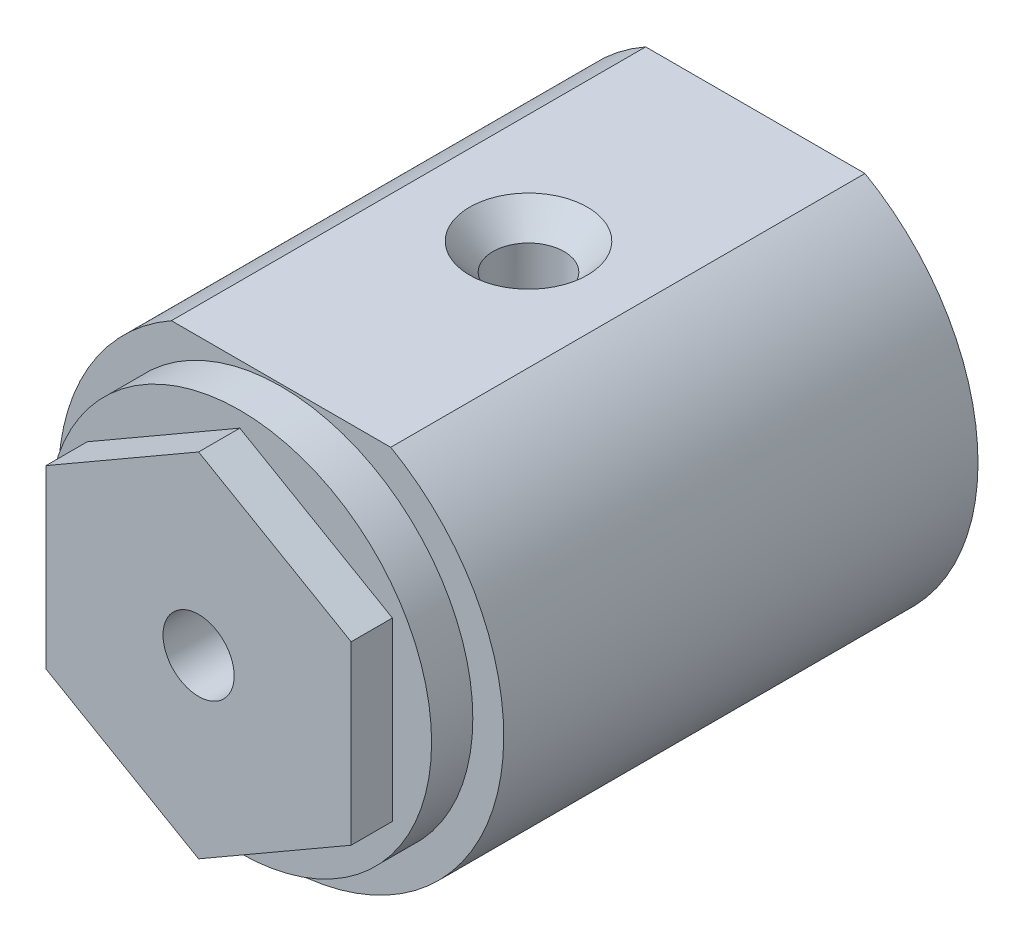
SolidWorks part; units mm, degrees
ref_plane "Front Plane" through (0, 0, 0) normal (0, 0, 1) x (1, 0, 0)
ref_plane "Top Plane" through (0, 0, 0) normal (0, 1, 0) x (1, 0, 0)
ref_plane "Right Plane" through (0, 0, 0) normal (1, 0, 0) x (0, 0, -1)
sketch "Base" plane through (0, 0, 0) normal (0, 0, 1) x (1, 0, 0)
  line L0 (-5.2536, 5.9) -> (5.2536, 5.9)
  line L1 (-5.3179, 9.4) -> (5.3179, 9.4)
  arc A0 (-5.3179, 9.4) -> (5.3179, 9.4) centre (0, 0) ccw
  arc A1 (-5.2536, 5.9) -> (5.2536, 5.9) centre (0, 0) ccw
  point P6 (0, -7.9)
  dimension "D1" = 10.8
  dimension "D2" = 3.5
  dimension "D4" = 7.9
  dimension "D3" = 13.8
extrude "Boss-Extrude1" add sketch "Base" along normal blind 23
ref_plane "Chamfer Plane" through (0, 9.4, 0) normal (0, 1, 0) x (1, 0, 0)
sketch "Screw Hole" plane through (0, 9.4, 0) normal (0, 1, 0) x (1, 0, 0)
  line L0 (5.3179, 0) -> (-5.3179, 0) construction
  circle A0 centre (0, -11) radius 1.8
  point P2 (0, 0)
  dimension "D1" = 3.6
  dimension "D2" = 11
hole_wizard "CSK for #4 Flat Head Machine Screw1" positions "Sketch4" profile "Sketch3" countersink size "#4" standard "ANSI Inch" end condition up to next
sketch "Sketch4" plane through (0, 9.4, 0) normal (0, 1, 0) x (1, 0, 0)
  point P0 (0, -11)
sketch "Sketch3" plane through (0, 9.4, 11) normal (1, 0, 0) x (0, 0, 1)
  line L0 (0, 0) -> (0, 3.5)
  line L1 (0, 3.5) -> (1.7272, 3.5)
  line L2 (1.7272, 3.5) -> (1.7272, 1.3003)
  line L3 (1.7272, 1.3003) -> (2.8575, 0)
  line L5 (2.8575, 0) -> (0, 0)
  line L6 (-1.7272, 1.3003) -> (-2.8575, 0) construction
  line L11 (0, -6.35) -> (0, 107.95) construction
  dimension "Thru Hole Dia." = 3.4544
  dimension "Thru Hole Depth" = 3.5
  dimension "Near C'Sink Dia." = 5.715
  dimension "Near C'Sink Angle" = 82
ref_plane "Plane1" through (0, 0, 23) normal (0, 0, 1) x (1, 0, 0)
sketch "Sketch5" plane through (0, 0, 23) normal (0, 0, 1) x (1, 0, 0)
  circle A0 centre (0, 0) radius 9.3
extrude "Boss-Extrude2" add sketch "Sketch5" along normal blind 2 and the other way blind 4
ref_plane "Plane2" through (0, 0, 25) normal (0, 0, 1) x (1, 0, 0)
sketch "Sketch6" plane through (0, 0, 25) normal (0, 0, 1) x (1, 0, 0)
  line L1 (0, 8.5448) -> (-7.4, 4.2724)
  line L2 (-7.4, 4.2724) -> (-7.4, -4.2724)
  line L3 (-7.4, -4.2724) -> (0, -8.5448)
  line L4 (0, -8.5448) -> (7.4, -4.2724)
  line L5 (7.4, -4.2724) -> (7.4, 4.2724)
  line L6 (7.4, 4.2724) -> (0, 8.5448)
  circle A0 centre (0, 0) radius 7.4 construction
  dimension "D1" = 14.8
extrude "Boss-Extrude3" add sketch "Sketch6" along normal blind 2
ref_plane "Plane3" through (0, 0, 19) normal (0, 0, -1) x (-1, 0, 0)
sketch "Sketch7" plane through (0, 0, 19) normal (0, 0, -1) x (-1, 0, 0)
  line L1 (0, 3.8682) -> (-3.35, 1.9341)
  line L2 (-3.35, 1.9341) -> (-3.35, -1.9341)
  line L3 (-3.35, -1.9341) -> (0, -3.8682)
  line L4 (0, -3.8682) -> (3.35, -1.9341)
  line L5 (3.35, -1.9341) -> (3.35, 1.9341)
  line L6 (3.35, 1.9341) -> (0, 3.8682)
  circle A0 centre (0, 0) radius 3.35 construction
  dimension "D1" = 6.7
extrude "Cut-Extrude1" cut sketch "Sketch7" against normal blind 3.6
sketch "Sketch8" plane through (0, 0, 19) normal (0, 0, -1) x (-1, 0, 0)
  circle A0 centre (0, 0) radius 1.725
  dimension "D1" = 3.45
extrude "Cut-Extrude2" cut sketch "Sketch8" against normal through all
